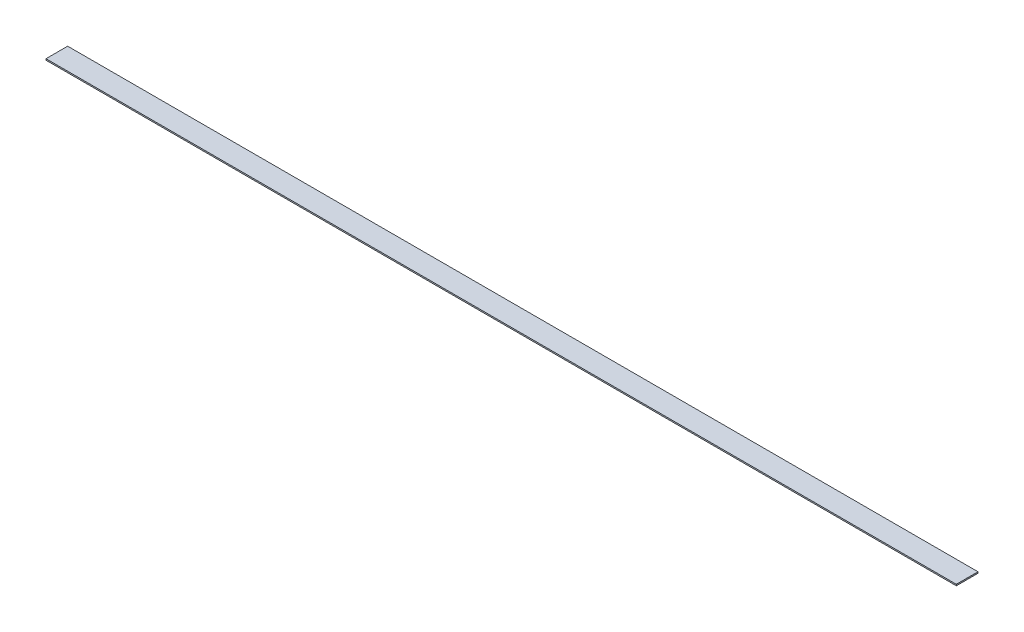
SolidWorks part; units mm, degrees
ref_plane "Front Plane" through (0, 0, 0) normal (0, 0, 1) x (1, 0, 0)
ref_plane "Top Plane" through (0, 0, 0) normal (0, 1, 0) x (1, 0, 0)
ref_plane "Right Plane" through (0, 0, 0) normal (1, 0, 0) x (0, 0, -1)
sketch "Sketch1" plane through (0, 0, 0) normal (0, 1, 0) x (1, 0, 0)
  line L1 (0, 0) -> (1066.8, 0)
  line L2 (0, 0) -> (0, 25.4)
  line L3 (0, 25.4) -> (1066.8, 25.4)
  line L4 (1066.8, 0) -> (1066.8, 25.4)
  dimension "D1" = 25.4
  dimension "D2" = 1066.8
extrude "Boss-Extrude1" add sketch "Sketch1" along normal blind 1.5875
